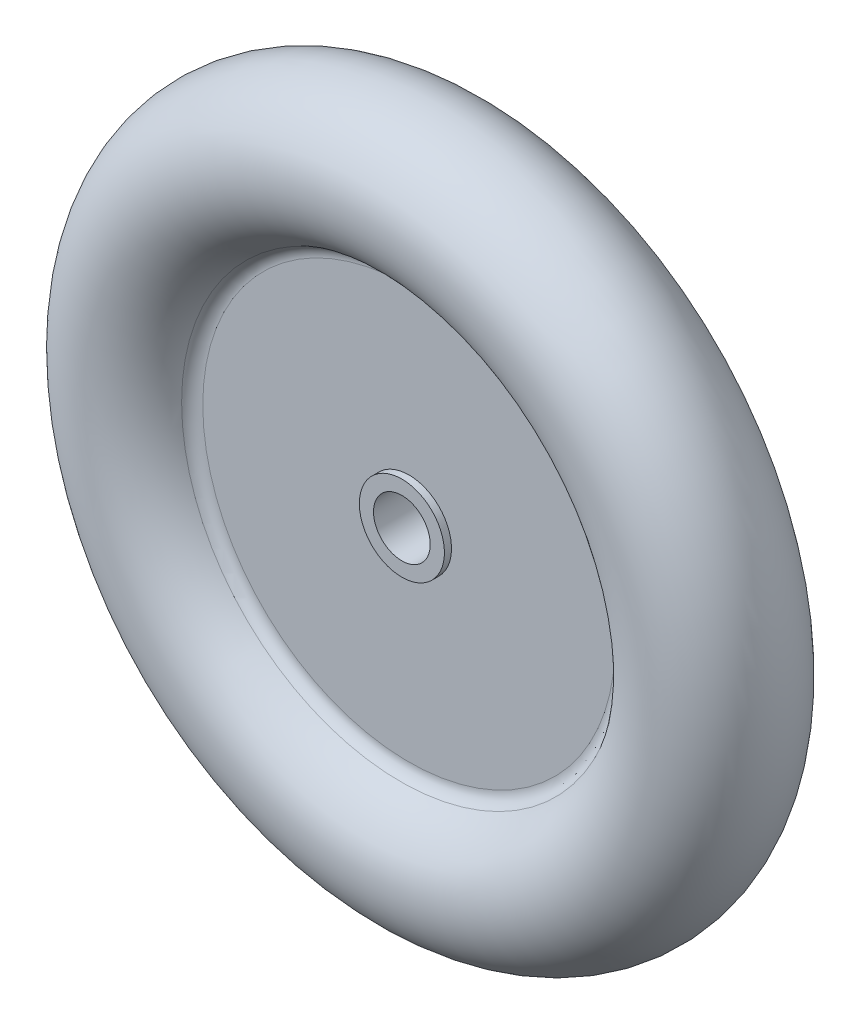
SolidWorks part; units mm, degrees
material "Pine"
ref_plane "Front" through (0, 0, 0) normal (0, 0, 1) x (1, 0, 0)
ref_plane "Top" through (0, 0, 0) normal (0, 1, 0) x (1, 0, 0)
ref_plane "Right" through (0, 0, 0) normal (1, 0, 0) x (0, 0, -1)
sketch "Sketch1" plane through (0, 0, 0) normal (1, 0, 0) x (0, 0, -1)
  line L0 (-1.5, 3) -> (-2, 3)
  line L1 (18.1622, 0) -> (-17.139, 0) construction
  line L2 (2, 2) -> (-2, 2)
  line L3 (2, 2) -> (2, 3)
  line L4 (-2, 2) -> (-2, 3)
  line L5 (1.5, 3) -> (1.5, 14.5456)
  line L6 (-1.5, 3) -> (-1.5, 14.5456)
  line L7 (2, 3) -> (1.5, 3)
  line L10 (18.1622, 3) -> (-17.139, 3) construction
  line L11 (18.1622, 2) -> (-17.139, 2) construction
  arc A0 (2.0833, 15.4547) -> (1.5, 14.5456) centre (2.5, 14.5456) ccw
  arc A1 (2.0833, 15.4547) -> (-2.0833, 15.4547) centre (0, 20) ccw
  arc A2 (-1.5, 14.5456) -> (-2.0833, 15.4547) centre (-2.5, 14.5456) ccw
revolve "Revolve1" add sketch "Sketch1" angle 360 about L1
